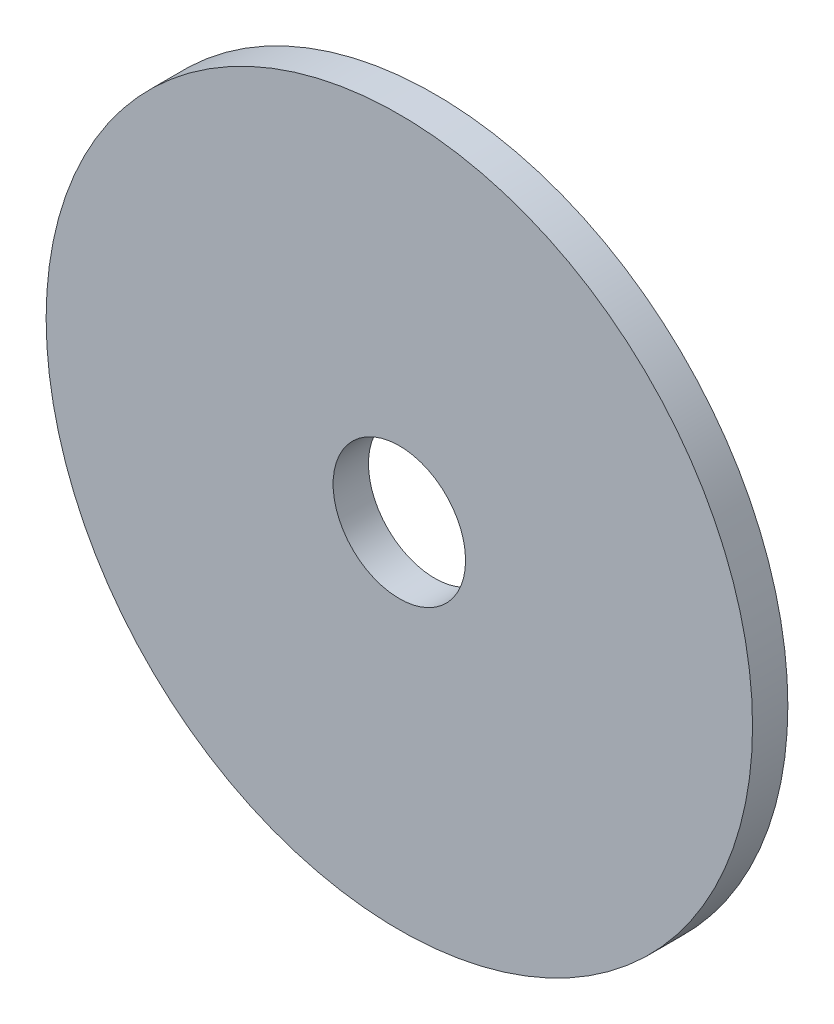
SolidWorks part; units mm, degrees
material "AISI 1020"
ref_plane "Front Plane" through (0, 0, 0) normal (0, 0, 1) x (1, 0, 0)
ref_plane "Top Plane" through (0, 0, 0) normal (0, 1, 0) x (1, 0, 0)
ref_plane "Right Plane" through (0, 0, 0) normal (1, 0, 0) x (0, 0, -1)
sketch "Sketch1" plane through (0, 0, 0) normal (0, 0, 1) x (1, 0, 0)
  circle A0 centre (0, 0) radius 2.3813
  circle A1 centre (0, 0) radius 12.7
  dimension "D1" = 4.7625
  dimension "D2" = 25.4
extrude "Boss-Extrude1" add sketch "Sketch1" along normal blind 1.27
